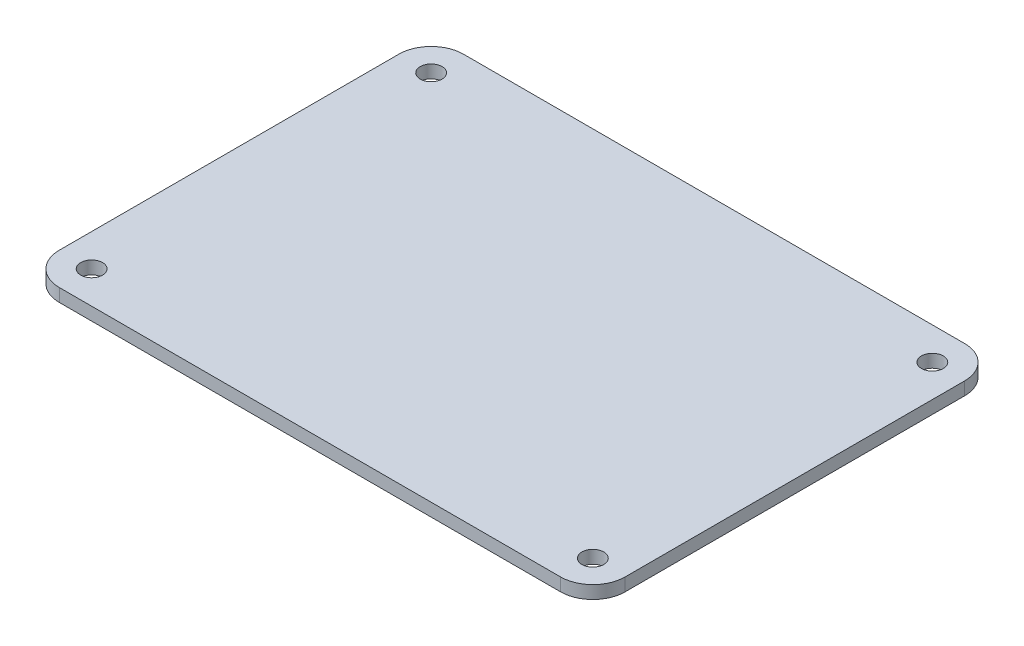
SolidWorks part; units mm, degrees
ref_plane "Front Plane" through (0, 0, 0) normal (0, 0, 1) x (1, 0, 0)
ref_plane "Top Plane" through (0, 0, 0) normal (0, 1, 0) x (1, 0, 0)
ref_plane "Right Plane" through (0, 0, 0) normal (1, 0, 0) x (0, 0, -1)
sketch "Sketch1" plane through (0, 0, 0) normal (0, 1, 0) x (1, 0, 0)
  line L1 (-35, -25) -> (35, -25)
  line L2 (-35, -25) -> (-35, 25)
  line L3 (-35, 25) -> (35, 25)
  line L4 (35, -25) -> (35, 25)
  line L5 (-35, -25) -> (35, 25) construction
  line L6 (-35, 25) -> (35, -25) construction
  point P0 (0, 0)
  dimension "D1" = 70
  dimension "D2" = 50
extrude "Boss-Extrude1" add sketch "Sketch1" along normal blind 1.6
sketch "Sketch2" plane through (0, 1.6, 0) normal (0, 1, 0) x (1, 0, 0)
  line L0 (-35, 25) -> (-35, -25) construction
  line L1 (-31, -21) -> (31, -21) construction
  line L2 (-31, -21) -> (-31, 21) construction
  line L3 (-31, 21) -> (31, 21) construction
  line L4 (31, -21) -> (31, 21) construction
  line L5 (-31, -21) -> (31, 21) construction
  line L6 (-31, 21) -> (31, -21) construction
  line L7 (35, 25) -> (-35, 25) construction
  circle A0 centre (-31, 21) radius 1.35
  circle A1 centre (31, 21) radius 1.35
  circle A2 centre (31, -21) radius 1.35
  circle A3 centre (-31, -21) radius 1.35
  point P0 (0, 0)
  dimension "D1" = 2.7
  dimension "D2" = 4
  dimension "D3" = 4
extrude "Cut-Extrude1" cut sketch "Sketch2" against normal through all
fillet "Fillet1" radius 4 4 edges at (35, 0.8, -25) (35, 0.8, 25) (-35, 0.8, 25) (-35, 0.8, -25)
